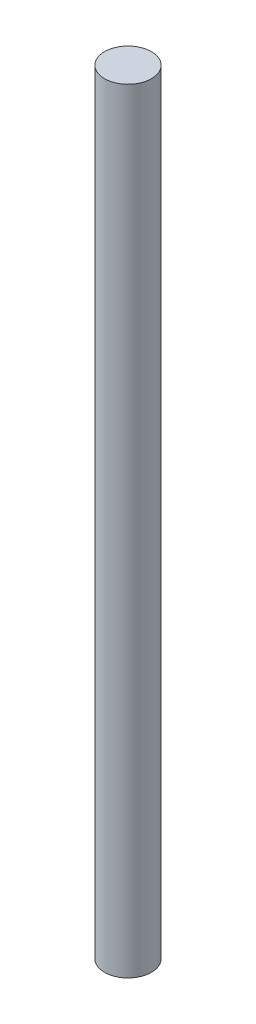
SolidWorks part; units mm, degrees
ref_plane "Alzado" through (0, 0, 0) normal (0, 0, 1) x (1, 0, 0)
ref_plane "Planta" through (0, 0, 0) normal (0, 1, 0) x (1, 0, 0)
ref_plane "Vista lateral" through (0, 0, 0) normal (1, 0, 0) x (0, 0, -1)
sketch "Croquis1" plane through (0, 0, 0) normal (0, 1, 0) x (1, 0, 0)
  circle A0 centre (0, 0) radius 3.15
  dimension "D1" = 6.3
extrude "Saliente-Extruir1" add sketch "Croquis1" along normal blind 104
